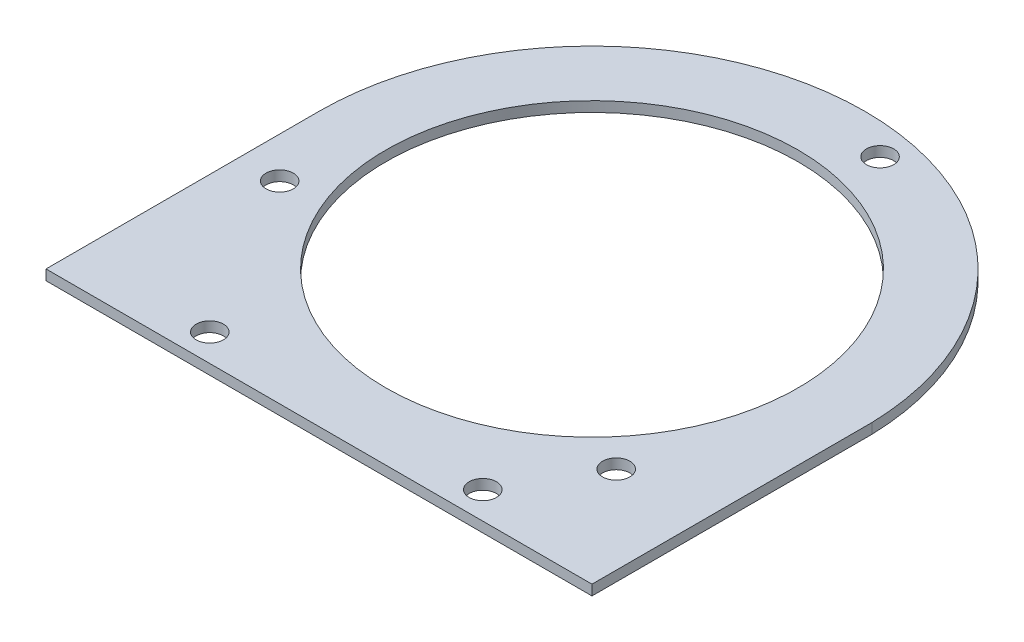
SolidWorks part; units mm, degrees
ref_plane "Front Plane" through (0, 0, 0) normal (0, 0, 1) x (1, 0, 0)
ref_plane "Top Plane" through (0, 0, 0) normal (0, 1, 0) x (1, 0, 0)
ref_plane "Right Plane" through (0, 0, 0) normal (1, 0, 0) x (0, 0, -1)
sketch "Sketch1" plane through (0, 0, 0) normal (0, 1, 0) x (1, 0, 0)
  line L0 (0, 114.3) -> (0, -101.6) construction
  line L1 (-127, -114.3) -> (127, -114.3) construction
  line L4 (-127, 0) -> (-127, -101.6) construction
  line L10 (127, -127) -> (-127, -127)
  line L12 (127, -127) -> (127, 3.175)
  line L14 (-127, -127) -> (-127, 0)
  circle A0 centre (0, 0) radius 95.885
  circle A1 centre (0, 0) radius 114.3 construction
  circle A2 centre (-108.0728, -37.2124) radius 6.35
  arc A3 (-127, 0) -> (0, 127) centre (0, 0) cw
  arc A4 (0, 127) -> (127, 3.175) centre (0, -0.0407) cw
  circle A5 centre (21.8095, 112.2) radius 6.35
  circle A6 centre (86.2633, -74.9875) radius 6.35
  circle A7 centre (-63.5, -114.3) radius 6.35
  circle A8 centre (63.5, -114.3) radius 6.35
  point P0 (0, 0)
  point P11 (0, 0)
  point P46 (0, 0)
  dimension "D3" = 191.77
  dimension "D5" = 228.6
  dimension "D6" = 12.7
  dimension "D7" = 127
  dimension "D8" = 127.0407
  dimension "D11" = 63.5
  dimension "D9" = 12.7
  dimension "D10" = 12.7
  dimension "D2" = 127
  dimension "D4" = 127
  dimension "D18" = 127
extrude "Boss-Extrude1" add sketch "Sketch1" along normal blind 4.7625
